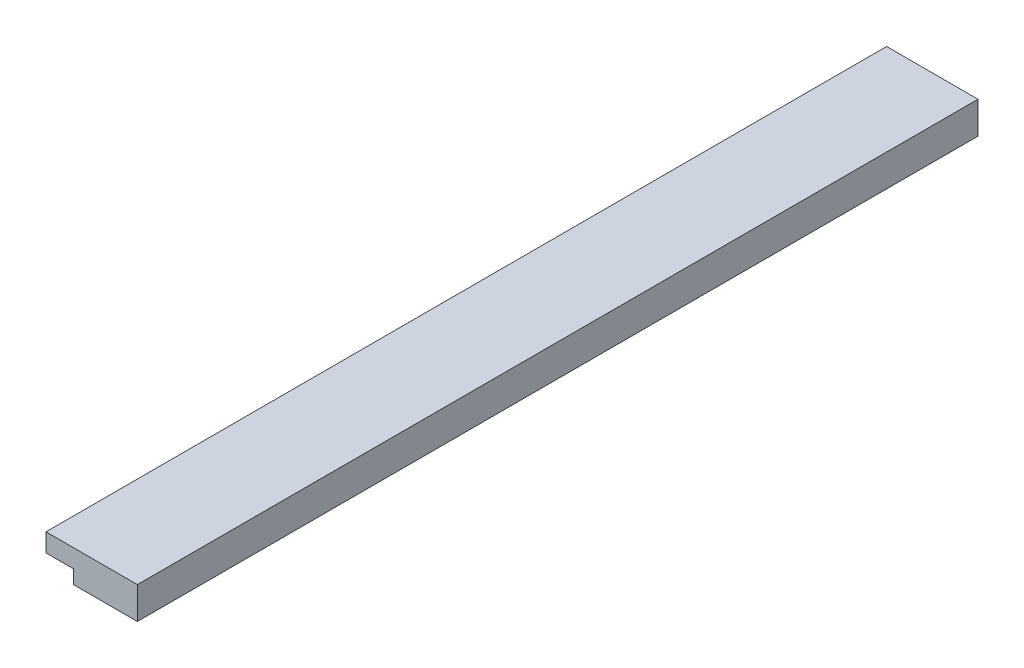
SolidWorks part; units mm, degrees
ref_plane "Front Plane" through (0, 0, 0) normal (0, 0, 1) x (1, 0, 0)
ref_plane "Top Plane" through (0, 0, 0) normal (0, 1, 0) x (1, 0, 0)
ref_plane "Right Plane" through (0, 0, 0) normal (1, 0, 0) x (0, 0, -1)
sketch "스케치1" plane through (0, 0, 0) normal (0, 1, 0) x (1, 0, 0)
  line L1 (-5, -46) -> (5, -46)
  line L2 (-5, -46) -> (-5, 46)
  line L3 (-5, 46) -> (5, 46)
  line L4 (5, -46) -> (5, 46)
  dimension "D1" = 92
  dimension "D2" = 46
  dimension "D3" = 10
  dimension "D4" = 5
extrude "보스-돌출1" add sketch "스케치1" along normal blind 3.5
sketch "스케치2" plane through (0, 0, 0) normal (0, -1, 0) x (1, 0, 0)
  line L0 (0, 0) -> (-50000, 0) construction
  line L1 (-0.7139, 40) -> (-50000.7139, 40) construction
  line L2 (1.1898, -40) -> (-49998.8102, -40) construction
  line L3 (5, 46) -> (5, -46) construction
  line L4 (5, 43.5) -> (-2, 43.5)
  line L5 (5, 43.5) -> (5, 36.5)
  line L6 (5, 36.5) -> (-2, 36.5)
  line L7 (-2, 43.5) -> (-2, 36.5)
  line L9 (5, 3.5) -> (-2, 3.5)
  line L10 (5, 3.5) -> (5, -3.5)
  line L11 (5, -3.5) -> (-2, -3.5)
  line L12 (-2, 3.5) -> (-2, -3.5)
  line L13 (5, -36.5) -> (-2, -36.5)
  line L14 (5, -36.5) -> (5, -43.5)
  line L15 (5, -43.5) -> (-2, -43.5)
  line L16 (-2, -36.5) -> (-2, -43.5)
  dimension "D1" = 40
  dimension "D2" = 40
  dimension "D3" = 7
  dimension "D4" = 7
  dimension "D5" = 3.5
  dimension "D6" = 7
  dimension "D7" = 7
  dimension "D8" = 3.5
  dimension "D9" = 7
  dimension "D10" = 7
  dimension "D11" = 3.5
extrude "보스-돌출2" add sketch "스케치2" along normal blind 7
sketch "스케치3" plane through (5, 0, 0) normal (1, 0, 0) x (0, 0, -1)
  line L0 (0, 0) -> (0, 50000) construction
  line L1 (40, -3.925) -> (40, 49996.075) construction
  line L2 (-40, -3.1895) -> (-40, 49996.8105) construction
  line L3 (-10.6648, -3.5) -> (49989.3352, -3.5) construction
  line L4 (3.5, 0) -> (36.5, 0) construction
  circle A0 centre (-40, -3.5) radius 1.5
  circle A1 centre (0, -3.5) radius 1.5
  circle A2 centre (40, -3.5) radius 1.5
  dimension "D1" = 40
  dimension "D2" = 40
  dimension "D3" = 3.5
extrude "컷-돌출1" cut sketch "스케치3" against normal blind 7
sketch "스케치4" plane through (-2, 0, 0) normal (-1, 0, 0) x (0, 0, 1)
  circle A0 centre (-40, -3.5) radius 2.15
  circle A1 centre (0, -3.5) radius 2.15
  circle A2 centre (40, -3.5) radius 2.15
extrude "컷-돌출2" cut sketch "스케치4" against normal blind 1
sketch "스케치5" plane through (0, 0, -46) normal (0, 0, -1) x (-1, 0, 0)
  line L1 (5, 0) -> (2, 0)
  line L2 (5, 0) -> (5, 1.5)
  line L3 (5, 1.5) -> (2, 1.5)
  line L4 (2, 0) -> (2, 1.5)
  dimension "D1" = 3
  dimension "D2" = 1.5
extrude "컷-돌출3" cut sketch "스케치5" against normal blind 92
sketch "스케치6" plane through (0, 0, 0) normal (0, -1, 0) x (1, 0, 0)
  line L1 (-18.779, 48.7998) -> (11.2419, 48.7998)
  line L2 (-18.779, 48.7998) -> (-18.779, -48.0333)
  line L3 (-18.779, -48.0333) -> (11.2419, -48.0333)
  line L4 (11.2419, 48.7998) -> (11.2419, -48.0333)
extrude "컷-돌출4" cut sketch "스케치6" along normal blind 10
